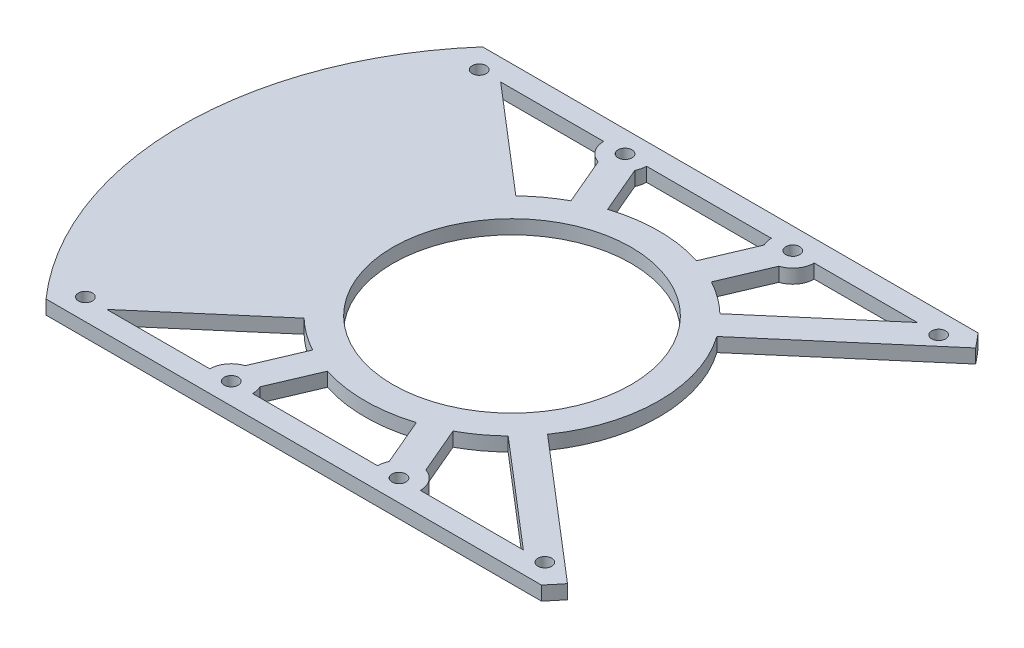
SolidWorks part; units mm, degrees
ref_plane "Front" through (0, 0, 0) normal (0, 0, 1) x (1, 0, 0)
ref_plane "Top" through (0, 0, 0) normal (0, 1, 0) x (1, 0, 0)
ref_plane "Right" through (0, 0, 0) normal (1, 0, 0) x (0, 0, -1)
sketch "Sketch1" plane through (0, 0, 0) normal (0, 1, 0) x (1, 0, 0)
  circle A0 centre (0, 0) radius 75
  circle A1 centre (0, 0) radius 75 construction
extrude "Boss-Extrude1" add sketch "Sketch1" along normal blind 3.175
sketch "Sketch2" plane through (0, 3.175, 0) normal (0, 1, 0) x (1, 0, 0)
  line L0 (-56.262, -49.5942) -> (56.262, -49.5942)
  line L1 (-56.262, 49.5942) -> (56.262, 49.5942)
  line L2 (56.262, -49.5942) -> (-56.262, -49.5942) construction
  circle A0 centre (0, 0) radius 75 construction
  arc A1 (-56.262, 49.5942) -> (56.262, 49.5942) centre (0, 0) cw
  arc A2 (-56.262, -49.5942) -> (56.262, -49.5942) centre (0, 0) ccw
extrude "Cut-Extrude1" cut sketch "Sketch2" against normal up to surface (3.175 mm away) up to face at (0, 0, 75)
sketch "Sketch3" plane through (0, 3.175, 0) normal (0, 1, 0) x (1, 0, 0)
  circle A0 centre (-52.1803, 44.7298) radius 1.5875
  circle A1 centre (-19.05, 44.7298) radius 1.5875
  circle A2 centre (19.05, 44.7298) radius 1.5875
  circle A3 centre (52.1803, 44.7298) radius 1.5875
  circle A4 centre (52.1803, -44.7298) radius 1.5875
  circle A5 centre (19.05, -44.7298) radius 1.5875
  circle A6 centre (-19.05, -44.7298) radius 1.5875
  circle A7 centre (-52.1803, -44.7298) radius 1.5875
  circle A8 centre (-52.1803, 44.7298) radius 1.5875 construction
  circle A9 centre (-52.1803, -44.7298) radius 1.5875 construction
  circle A10 centre (-19.05, -44.7298) radius 1.5875 construction
  circle A11 centre (19.05, -44.7298) radius 1.5875 construction
  circle A12 centre (52.1803, -44.7298) radius 1.5875 construction
  circle A13 centre (-19.05, 44.7298) radius 1.5875 construction
  circle A14 centre (19.05, 44.7298) radius 1.5875 construction
  circle A15 centre (52.1803, 44.7298) radius 1.5875 construction
extrude "Cut-Extrude2" cut sketch "Sketch3" against normal up to surface (3.175 mm away) up to face at (0, 0, 0)
sketch "Sketch4" plane through (0, 3.175, 0) normal (0, 1, 0) x (1, 0, 0)
  line L1 (-14.3617, -33.7216) -> (17.144, 40.2544) construction
  line L2 (-19.05, 44.7298) -> (19.05, -44.7298) construction
  line L3 (-52.1803, 44.7298) -> (52.1803, -44.7298) construction
  line L4 (52.1803, 44.7298) -> (-52.1803, -44.7298) construction
  line L6 (-47.3159, -44.7419) -> (-23.1778, -24.0503)
  line L7 (-15.9495, -29.3469) -> (-20.5271, -40.0951)
  line L8 (-10.1073, -31.835) -> (-14.6849, -42.5833)
  line L9 (10.1073, -31.835) -> (14.6849, -42.5833)
  line L10 (15.9495, -29.3469) -> (20.5271, -40.0951)
  line L11 (23.1778, -24.0503) -> (47.3159, -44.7419)
  line L13 (0, 0) -> (27.051, 0) construction
  line L15 (23.1778, 24.0503) -> (47.3159, 44.7419)
  line L16 (15.9495, 29.3469) -> (20.5271, 40.0951)
  line L17 (10.1073, 31.835) -> (14.6849, 42.5833)
  line L18 (-10.1073, 31.835) -> (-14.6849, 42.5833)
  line L19 (-15.9495, 29.3469) -> (-20.5271, 40.0951)
  line L20 (-47.3159, 44.7419) -> (-23.1778, 24.0503)
  line L22 (-47.3159, 44.7419) -> (-23.9144, 44.7419)
  line L23 (-14.1856, 44.7298) -> (14.1856, 44.7298)
  line L24 (23.1778, 44.7298) -> (23.9144, 44.7298)
  line L25 (23.9144, 44.7298) -> (47.3159, 44.7419)
  line L26 (-47.3159, -44.7419) -> (-23.9144, -44.7298)
  line L27 (-14.1856, -44.7298) -> (14.1856, -44.7298)
  line L28 (23.9144, -44.7298) -> (47.3159, -44.7419)
  circle A0 centre (0, 0) radius 27.051
  arc A1 (-15.9495, 29.3469) -> (-15.9495, -29.3469) centre (0, 0) ccw
  arc A2 (23.9144, -44.7298) -> (20.5271, -40.0951) centre (19.05, -44.7298) ccw
  arc A3 (14.6849, -42.5833) -> (14.1856, -44.7298) centre (19.05, -44.7298) ccw
  arc A4 (-14.1856, -44.7298) -> (-14.6849, -42.5833) centre (-19.05, -44.7298) ccw
  arc A5 (-20.5271, -40.0951) -> (-23.9144, -44.7298) centre (-19.05, -44.7298) ccw
  arc A6 (-14.6849, 42.5833) -> (-14.1856, 44.7298) centre (-19.05, 44.7298) ccw
  arc A7 (-23.9144, 44.7419) -> (-20.5271, 40.0951) centre (-19.05, 44.7298) ccw
  arc A8 (14.1856, 44.7298) -> (14.6849, 42.5833) centre (19.05, 44.7298) ccw
  arc A9 (10.1073, 31.835) -> (-10.1073, 31.835) centre (0, 0) ccw
  arc A10 (20.5271, 40.0951) -> (23.9144, 44.7298) centre (19.05, 44.7298) ccw
  arc A11 (15.9495, -29.3469) -> (15.9495, 29.3469) centre (0, 0) ccw
  arc A12 (-10.1073, -31.835) -> (10.1073, -31.835) centre (0, 0) ccw
  dimension "D1" = 54.102
  dimension "D2" = 6.35
  dimension "D4" = 6.35
extrude "Cut-Extrude3" cut sketch "Sketch4" against normal up to surface (3.175 mm away) contours A7 L22 L20 A1 L19 | A9 L17 A8 L23 A6 L18 | A11 L15 L25 A10 L16 | A0 | A5 L7 A1 L6 L26 | A12 L8 A4 L27 A3 L9 | A11 L10 A2 L28 L11 up to face at (-52.1803, 0, 46.3173)
sketch "Sketch5" plane through (0, 3.175, 0) normal (0, 1, 0) x (1, 0, 0)
  line L0 (58.9575, 46.3575) -> (27.3105, 19.2292)
  line L1 (23.1778, 24.0503) -> (47.3159, 44.7419) construction
  line L2 (27.3105, -19.2292) -> (58.9575, -46.3575)
  line L4 (23.1778, -24.0503) -> (47.3159, -44.7419) construction
  arc A0 (56.262, -49.5942) -> (56.262, 49.5942) centre (0, 0) ccw construction
  arc A1 (27.3105, 19.2292) -> (27.3105, -19.2292) centre (0, 0) cw
  arc A2 (23.1778, 24.0503) -> (15.9495, 29.3469) centre (0, 0) ccw construction
  arc A3 (58.9575, 46.3575) -> (58.9575, -46.3575) centre (0, 0) cw
  point P17 (-52.1803, 44.7298)
  dimension "D1" = 6.35
  dimension "D2" = 6.35
extrude "Cut-Extrude4" cut sketch "Sketch5" against normal up to surface (3.175 mm away) up to face at (0, 0, 39.9675)
